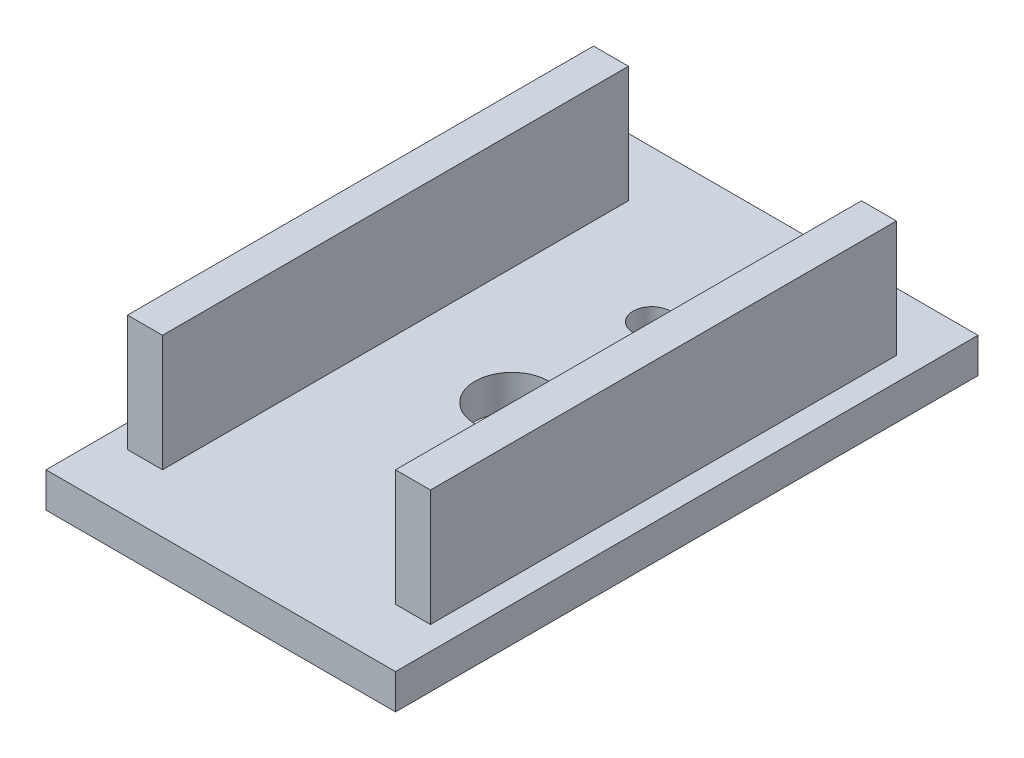
SolidWorks part; units mm, degrees
ref_plane "Plano frontal" through (0, 0, 0) normal (0, 0, 1) x (1, 0, 0)
ref_plane "Plano superior" through (0, 0, 0) normal (0, 1, 0) x (1, 0, 0)
ref_plane "Plano direito" through (0, 0, 0) normal (1, 0, 0) x (0, 0, -1)
sketch "Sketch1" plane through (0, 0, 0) normal (0, 1, 0) x (1, 0, 0)
  line L1 (-15, 25) -> (15, 25)
  line L2 (-15, 25) -> (-15, -25)
  line L3 (-15, -25) -> (15, -25)
  line L4 (15, 25) -> (15, -25)
  line L5 (-15, 25) -> (15, -25) construction
  line L6 (-15, -25) -> (15, 25) construction
  point P0 (0, 0)
  dimension "D1" = 50
  dimension "D2" = 30
extrude "Boss-Extrude1" add sketch "Sketch1" along normal mid plane 3
sketch "Sketch2" plane through (0, 1.5, 0) normal (0, 1, 0) x (1, 0, 0)
  circle A0 centre (0, 0) radius 3.175
  circle A1 centre (0, 12) radius 1.6
  point P5 (0, 0)
  dimension "D1" = 6.35
  dimension "D2" = 3.2
  dimension "D3" = 12
extrude "Cut-Extrude1" cut sketch "Sketch2" against normal up to surface (3 mm away) up to face at (0, -1.5, 0)
sketch "Sketch3" plane through (0, 1.5, 0) normal (0, 1, 0) x (1, 0, 0)
  line L1 (10, 20) -> (13, 20)
  line L2 (10, 20) -> (10, -20)
  line L3 (10, -20) -> (13, -20)
  line L4 (13, 20) -> (13, -20)
  point P4 (10, 0)
  dimension "D1" = 3
  dimension "D2" = 10
  dimension "D3" = 40
extrude "Boss-Extrude2" add sketch "Sketch3" along normal blind 10
mirror "Mirror1" about plane through (0, 0, 0) normal (1, 0, 0) of "Boss-Extrude2"
